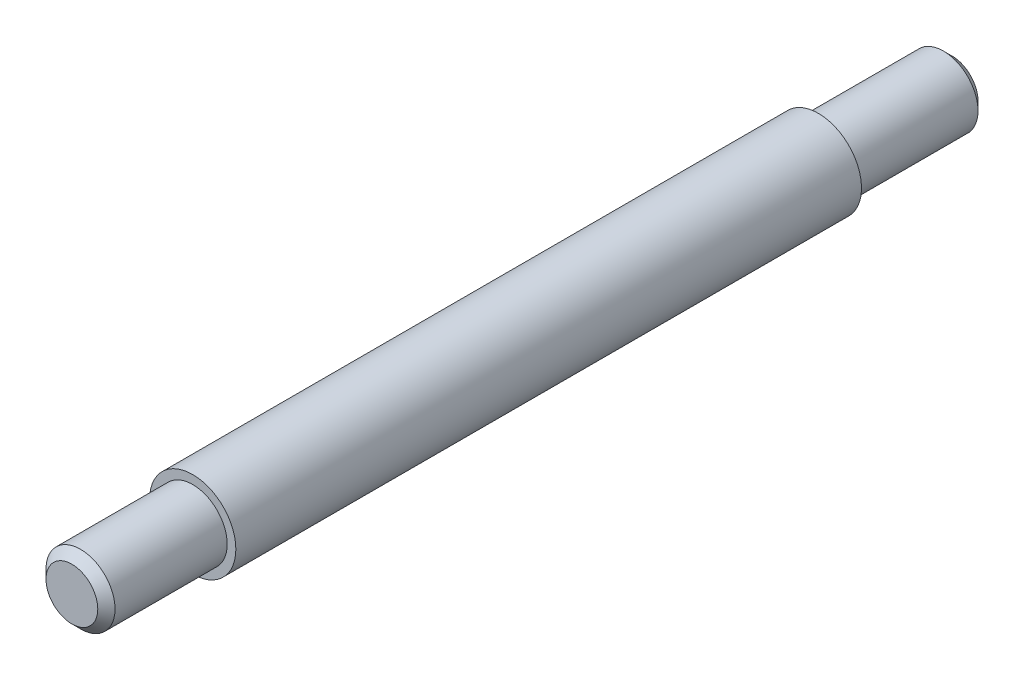
SolidWorks part; units mm, degrees
ref_plane "Ebene vorne" through (0, 0, 0) normal (0, 0, 1) x (1, 0, 0)
ref_plane "Ebene oben" through (0, 0, 0) normal (0, 1, 0) x (1, 0, 0)
ref_plane "Ebene rechts" through (0, 0, 0) normal (1, 0, 0) x (0, 0, -1)
sketch "Skizze1" plane through (0, 0, 0) normal (0, 0, 1) x (1, 0, 0)
  circle A0 centre (0, 0) radius 10
  dimension "D1" = 20
extrude "Aufsatz-Linear austragen1" add sketch "Skizze1" along normal blind 204
sketch "Skizze2" plane through (0, 0, 0) normal (0, 0, -1) x (-1, 0, 0)
  circle A0 centre (0, 0) radius 8
  circle A1 centre (0, 0) radius 10
  dimension "D1" = 16
  dimension "D2" = 20
extrude "Schnitt-Linear austragen1" cut sketch "Skizze2" against normal blind 31
cosmetic thread "Gewindedarstellung2" parameters "D1"=14, "D2"=13.797
sketch "Skizze3" plane through (0, 0, 204) normal (0, 0, 1) x (1, 0, 0)
  circle A0 centre (0, 0) radius 10
  circle A1 centre (0, 0) radius 8
  dimension "D1" = 16
  dimension "D2" = 20
extrude "Schnitt-Linear austragen2" cut sketch "Skizze3" against normal blind 28
cosmetic thread "Gewindedarstellung1" parameters "D1"=14, "D2"=13.797
chamfer "Fase1" distance 2 angle 45 1 edges at (8, 0, 204)
chamfer "Fase2" distance 2 angle 45 1 edges at (-8, 0, 0)
